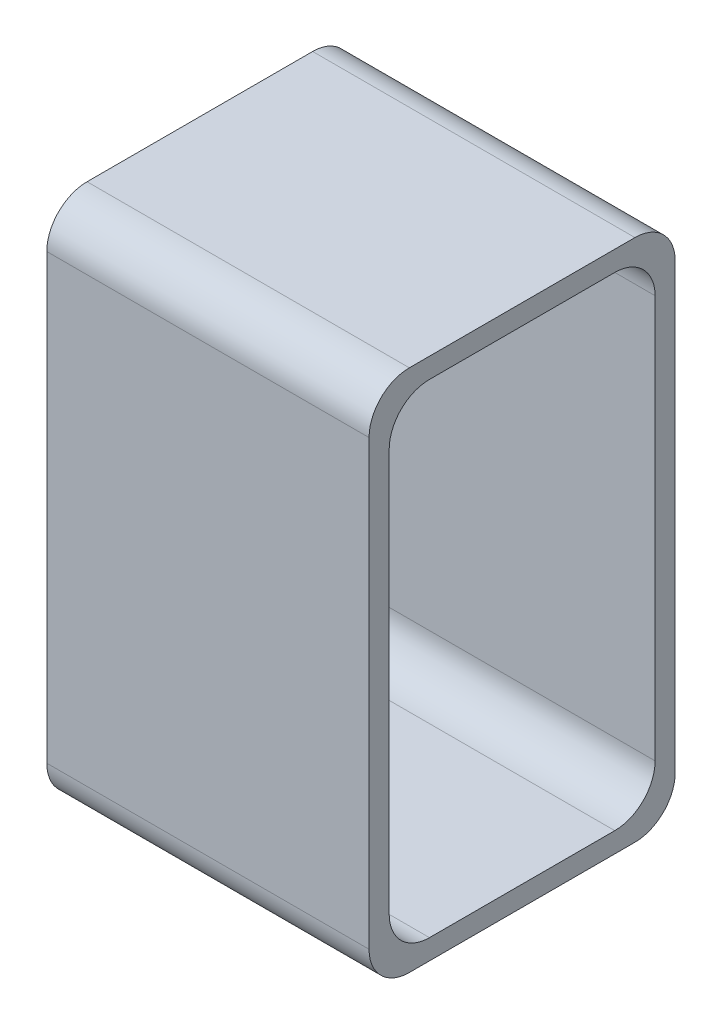
SolidWorks part; units mm, degrees
ref_plane "Front Plane" through (0, 0, 0) normal (0, 0, 1) x (1, 0, 0)
ref_plane "Top Plane" through (0, 0, 0) normal (0, 1, 0) x (1, 0, 0)
ref_plane "Right Plane" through (0, 0, 0) normal (1, 0, 0) x (0, 0, -1)
sketch "Sketch1" plane through (0, 0, 0) normal (0, 1, 0) x (1, 0, 0)
  line L1 (0, 0) -> (0.4, 0)
  line L2 (0, 0) -> (0, -0.38)
  line L3 (0, -0.38) -> (0.4, -0.38)
  line L4 (0.4, 0) -> (0.4, -0.38)
  dimension "D1" = 0.4
  dimension "D2" = 0.38
extrude "Boss-Extrude1" add sketch "Sketch1" along normal blind 0.65
sketch "Sketch2" plane through (0.4, 0, 0) normal (1, 0, 0) x (0, 0, -1)
  line L0 (-0.38, 0.65) -> (0, 0.65) construction
  line L1 (-0.355, 0.625) -> (-0.025, 0.625)
  line L2 (-0.355, 0.625) -> (-0.355, 0.025)
  line L3 (-0.355, 0.025) -> (-0.025, 0.025)
  line L4 (-0.025, 0.625) -> (-0.025, 0.025)
  line L5 (0, 0.65) -> (0, 0) construction
  point P6 (-0.19, 0.65)
  point P7 (-0.19, 0.625)
  point P10 (0, 0.325)
  point P11 (-0.025, 0.325)
  dimension "D1" = 0.33
  dimension "D2" = 0.6
extrude "Cut-Extrude1" cut sketch "Sketch2" against normal through all both and the other way through all
fillet "Fillet1" radius 0.05 8 edges at (0.2, 0.625, 0.355) (0.2, 0.625, 0.025) (0.2, 0.025, 0.355) (0.2, 0.025, 0.025) (0.2, 0.65, 0.38) (0.2, 0, 0.38) (0.2, 0, 0) (0.2, 0.65, 0)
sketch "Sketch4" plane through (0, 0, 0.025) normal (0, 0, 1) x (1, 0, 0)
  line L0 (0.2, 0.075) -> (0.2, 0.575) construction
  line L1 (0, 0.075) -> (0.4, 0.075) construction
  line L2 (0.4, 0.575) -> (0, 0.575) construction
  point P4 (0.2, 0.075)
  point P7 (0.2, 0.575)
